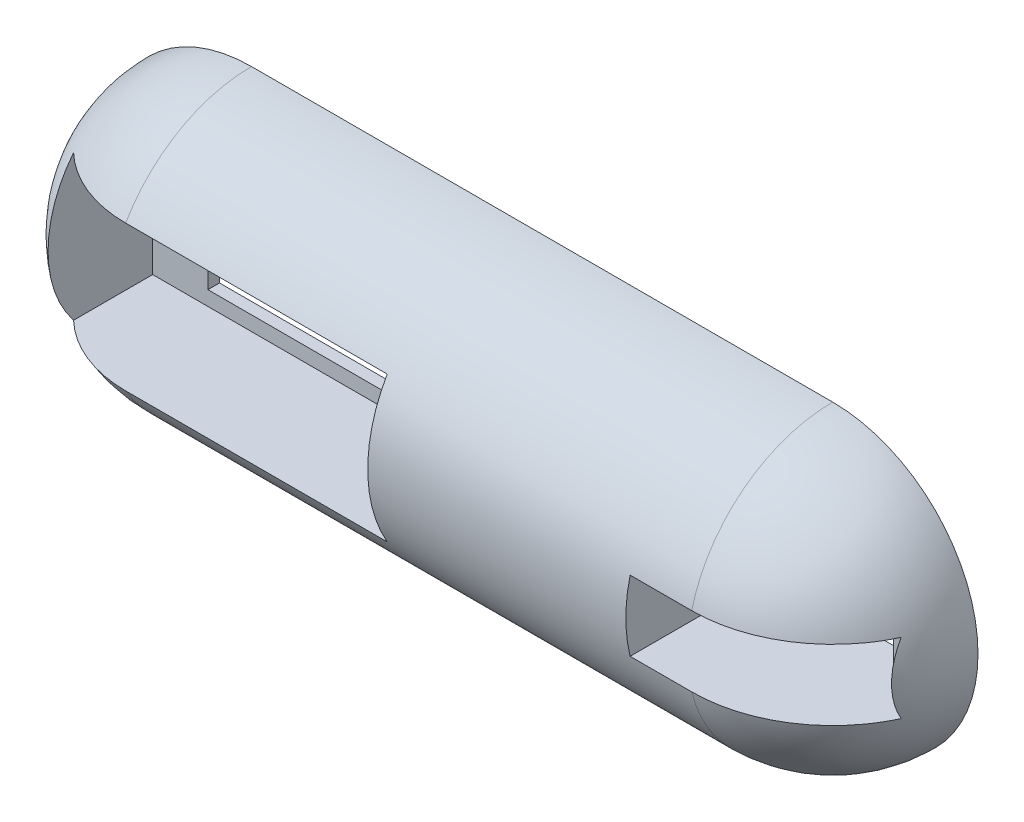
SolidWorks part; units mm, degrees
ref_plane "Ebene vorne" through (0, 0, 0) normal (0, 0, 1) x (1, 0, 0)
ref_plane "Ebene oben" through (0, 0, 0) normal (0, 1, 0) x (1, 0, 0)
ref_plane "Ebene rechts" through (0, 0, 0) normal (1, 0, 0) x (0, 0, -1)
sketch "Sketch1" plane through (0, 0, 0) normal (0, 0, 1) x (1, 0, 0)
  line L4 (-125, 0) -> (25, 0)
  line L5 (-100, 25) -> (0, 25)
  line L6 (-148.9192, 0) -> (153.2588, 0) construction
  arc A0 (25, 0) -> (0, 25) centre (0, 0) ccw
  arc A1 (-100, 25) -> (-125, 0) centre (-100, 0) ccw
  dimension "D1" = 25
  dimension "D3" = 25
  dimension "D2" = 150
  dimension "D4" = 25
  dimension "D5" = 25
revolve "Revolve1" add sketch "Sketch1" angle 180 about L4
sketch "Sketch3" plane through (0, 0, 0) normal (0, 0, -1) x (-1, 0, 0)
  line L1 (55, 12.5) -> (115, 12.5)
  line L2 (55, 12.5) -> (55, -12.5)
  line L3 (55, -12.5) -> (115, -12.5)
  line L4 (115, 12.5) -> (115, -12.5)
  arc A0 (100, -25) -> (100, 25) centre (100, 0) ccw construction
  point P6 (115, 0)
  point P9 (125, 0)
  dimension "D1" = 60
  dimension "D2" = 25
  dimension "D4" = 10
extrude "Cut-Extrude3" cut sketch "Sketch3" against normal through all from offset 2 offset against normal yes
sketch "Sketch7" plane through (0, 0, 2) normal (0, 0, 1) x (1, 0, 0)
  line L0 (-115, -12.5) -> (-115, 12.5) construction
  line L6 (-113.5, 10) -> (-57.5, 10) construction
  line L7 (-57.5, 10) -> (-57.5, -10) construction
  line L8 (-57.5, -10) -> (-113.5, -10) construction
  line L9 (-113.5, -10) -> (-113.5, 10) construction
  line L10 (-105.5, 10) -> (-65.5, 10)
  line L11 (-105.5, 10) -> (-105.5, -10)
  line L12 (-105.5, -10) -> (-65.5, -10)
  line L13 (-65.5, 10) -> (-65.5, -10)
  circle A0 centre (-109.5, 5) radius 2
  circle A1 centre (-61.5, 5) radius 2
  circle A2 centre (-109.5, -5) radius 2
  circle A3 centre (-61.5, -5) radius 2
  circle A4 centre (-95.5, -0.25) radius 3
  point P4 (-113.5, 0)
  point P7 (-115, 0)
  point P20 (0, 0)
  point P21 (0, 0)
  dimension "D4" = 4
  dimension "D10" = 4
  dimension "D14" = 6
  dimension "D2" = 56
  dimension "D3" = 20
  dimension "D5" = 1.5
  dimension "D6" = 5
  dimension "D11" = 14
  dimension "D12" = 10.25
  dimension "D13" = 4
  dimension "D15" = 5
  dimension "D16" = 40
  dimension "D17" = 4
  dimension "D7" = 2
  dimension "D8" = 2
  dimension "D9" = 2
extrude "Cut-Extrude8" cut sketch "Sketch7" against normal blind 10 contours A4 | L11 L10 L13 L12 | A0 | A2 | A3 | A1
ref_plane "Plane1" through (0, -25, 0) normal (0, -1, 0) x (-1, 0, 0)
sketch "Sketch10" plane through (0, -25, 0) normal (0, -1, 0) x (-1, 0, 0)
  line L0 (0, 0) -> (-25, 0)
  line L1 (-25, 0) -> (-25, -25)
  line L2 (-25, -25) -> (35, -25)
  line L3 (35, -25) -> (35, 0)
  line L4 (0, 0) -> (100, 0) construction
  line L5 (35, 0) -> (0, 0)
  dimension "D1" = 60
  dimension "D2" = 25
extrude "Cut-Extrude10" [suppressed] cut sketch "Sketch10" against normal blind 25
sketch "Sketch11" [suppressed] plane through (0, 0, 0) normal (0, -1, 0) x (1, 0, 0)
  line L1 (-35, 18.55) -> (-35, 6.45) construction
  line L2 (-35, 6.45) -> (-2.4, 6.45) construction
  line L3 (-2.4, 6.45) -> (-2.4, 18.55) construction
  line L4 (-2.4, 18.55) -> (-35, 18.55) construction
  line L5 (-35, 0) -> (-35, 25) construction
  line L6 (-35, 0) -> (25, 0) construction
  line L7 (-18.7, 18.55) -> (-18.7, 6.45) construction
  line L8 (-35, 12.5) -> (-2.4, 12.5) construction
  line L10 (-30.45, 18.55) -> (-6.95, 18.55)
  line L11 (-30.45, 18.55) -> (-30.45, 6.45)
  line L12 (-30.45, 6.45) -> (-6.95, 6.45)
  line L13 (-6.95, 18.55) -> (-6.95, 6.45)
  circle A0 centre (-32.95, 12.5) radius 1
  circle A1 centre (-4.45, 12.5) radius 1
  point P6 (-2.4, 12.5)
  point P22 (-18.7, 18.55)
  dimension "D7" = 2
  dimension "D1" = 32.6
  dimension "D2" = 12.1
  dimension "D3" = 0
  dimension "D4" = 12.5
  dimension "D5" = 2.05
  dimension "D6" = 6.05
  dimension "D8" = 12.1
  dimension "D9" = 23.5
extrude "Cut-Extrude11" [suppressed] cut sketch "Sketch11" against normal blind 28.8
sketch "Sketch12" [suppressed] plane through (0, 0, 0) normal (0, -1, 0) x (1, 0, 0)
  line L0 (-30.45, 18.55) -> (-30.45, 6.45)
  line L2 (-30.45, 6.45) -> (-35, 6.45)
  line L3 (-35, 0) -> (-35, 25) construction
  line L4 (-35, 6.45) -> (-35, 18.55)
  line L5 (-35, 18.55) -> (-30.45, 18.55)
  line L6 (-6.95, 6.45) -> (-2.4, 6.45)
  line L7 (-2.4, 6.45) -> (-2.4, 18.55)
  line L8 (-2.4, 18.55) -> (-6.95, 18.55)
  line L9 (-6.95, 18.55) -> (-6.95, 6.45)
  dimension "D1" = 4.55
extrude "Cut-Extrude12" [suppressed] cut sketch "Sketch12" against normal blind 8.7
sketch "Sketch13" plane through (0, 0, 0) normal (0, 0, -1) x (-1, 0, 0)
  line L0 (71.2, 25) -> (71.2, -25)
  line L1 (0, 25) -> (100, 25) construction
  line L2 (-13.3413, -25) -> (13.3413, -25) construction
  line L3 (71.2, -25) -> (51.2, -25)
  line L4 (51.2, -25) -> (51.2, 25)
  line L5 (51.2, 25) -> (71.2, 25)
  line L8 (61.2, 41.9012) -> (61.2, -41.1281) construction
  point P6 (61.2, 25)
  dimension "D1" = 20
  dimension "D2" = 28.8
extrude "Boss-Extrude1" [suppressed] add sketch "Sketch13" along normal blind 30
sketch "Sketch14" [suppressed] plane through (-70.575, 0, 0) normal (-1, 0, 0) x (0, 0, 1)
  line L0 (-30, -25) -> (0, -25) construction
  line L1 (-30, 25) -> (-25, 25)
  line L2 (-30, 25) -> (-30, -25)
  line L3 (-30, -25) -> (-25, -25)
  line L4 (-25, 25) -> (-25, -25)
  line L5 (0, -25) -> (0, 25) construction
  dimension "D1" = 25
extrude "Boss-Extrude2" [suppressed] add sketch "Sketch14" along normal blind 30
fillet "Fillet1" [suppressed] radius 10
fillet "Fillet2" [suppressed] radius 10
fillet "Fillet3" [suppressed] radius 10
sketch "Sketch16" plane through (0, 0, 0) normal (0, 0, 1) x (1, 0, 0)
  line L0 (-10.6, 6.05) -> (-10.6, -6.05) construction
  line L1 (-10.6, -6.05) -> (22, -6.05) construction
  line L2 (22, -6.05) -> (22, 6.05) construction
  line L3 (22, 6.05) -> (-10.6, 6.05) construction
  line L4 (5.7, 6.05) -> (5.7, -6.05) construction
  line L5 (-10.6, 0) -> (0, 0) construction
  line L6 (-6.05, 6.05) -> (17.45, 6.05)
  line L7 (-6.05, 6.05) -> (-6.05, -6.05)
  line L8 (-6.05, -6.05) -> (17.45, -6.05)
  line L9 (17.45, 6.05) -> (17.45, -6.05)
  circle A0 centre (-8.55, 0) radius 1
  circle A1 centre (19.95, 0) radius 1
  arc A2 (0, -25) -> (0, 25) centre (0, 0) ccw construction
  point P17 (5.7, 6.05)
  point P21 (25, 0)
  dimension "D5" = 2
  dimension "D1" = 32.6
  dimension "D2" = 12.1
  dimension "D3" = 2.05
  dimension "D4" = 6.05
  dimension "D6" = 12.1
  dimension "D7" = 23.5
  dimension "D8" = 3
extrude "Cut-Extrude13" cut sketch "Sketch16" along direction (0, 0, -1) on the side against the normal blind 23 from offset 25
sketch "Sketch18" plane through (0, 0, 0) normal (0, 0, -1) x (-1, 0, 0)
  line L0 (-17.45, 6.05) -> (-17.45, -6.05)
  line L1 (-17.45, -6.05) -> (-22, -6.05)
  line L2 (-22, -6.05) -> (-22, 6.05)
  line L3 (-22, 6.05) -> (-17.45, 6.05)
  line L4 (6.05, -6.05) -> (10.6, -6.05)
  line L5 (10.6, -6.05) -> (10.6, 6.05)
  line L6 (10.6, 6.05) -> (6.05, 6.05)
  line L7 (6.05, 6.05) -> (6.05, -6.05)
  line L8 (-22, -6.05) -> (-22, 6.05) construction
  point P16 (-17.45, 0)
  point P18 (6.05, 0)
  dimension "D1" = 4.55
  dimension "D2" = 12.1
  dimension "D3" = 12.1
  dimension "D4" = 23.5
  dimension "D6" = 4.55
extrude "Cut-Extrude14" cut sketch "Sketch18" against normal through all from offset 7 offset against normal yes
sketch "Sketch19" plane through (0, 0, 2) normal (0, 0, 1) x (1, 0, 0)
  line L0 (22, 6.05) -> (22, -6.05) construction
  circle A0 centre (11, 0) radius 2.5
  dimension "D1" = 5
  dimension "D2" = 11
extrude "Cut-Extrude15" cut sketch "Sketch19" against normal through all
sketch "Skizze1" plane through (0, 0, 2) normal (0, 0, 1) x (1, 0, 0)
  circle A0 centre (-95.5, -0.25) radius 4.4898
extrude "Schnitt-Linear austragen1" cut sketch "Skizze1" against normal blind 10
sketch "Skizze2" plane through (0, 0, 2) normal (0, 0, 1) x (1, 0, 0)
  line L1 (-6.05, 6.05) -> (17.45, 6.05)
  line L2 (-6.05, 6.05) -> (-6.05, -6.05)
  line L3 (-6.05, -6.05) -> (17.45, -6.05)
  line L4 (17.45, 6.05) -> (17.45, -6.05)
extrude "Schnitt-Linear austragen2" cut sketch "Skizze2" against normal blind 10
